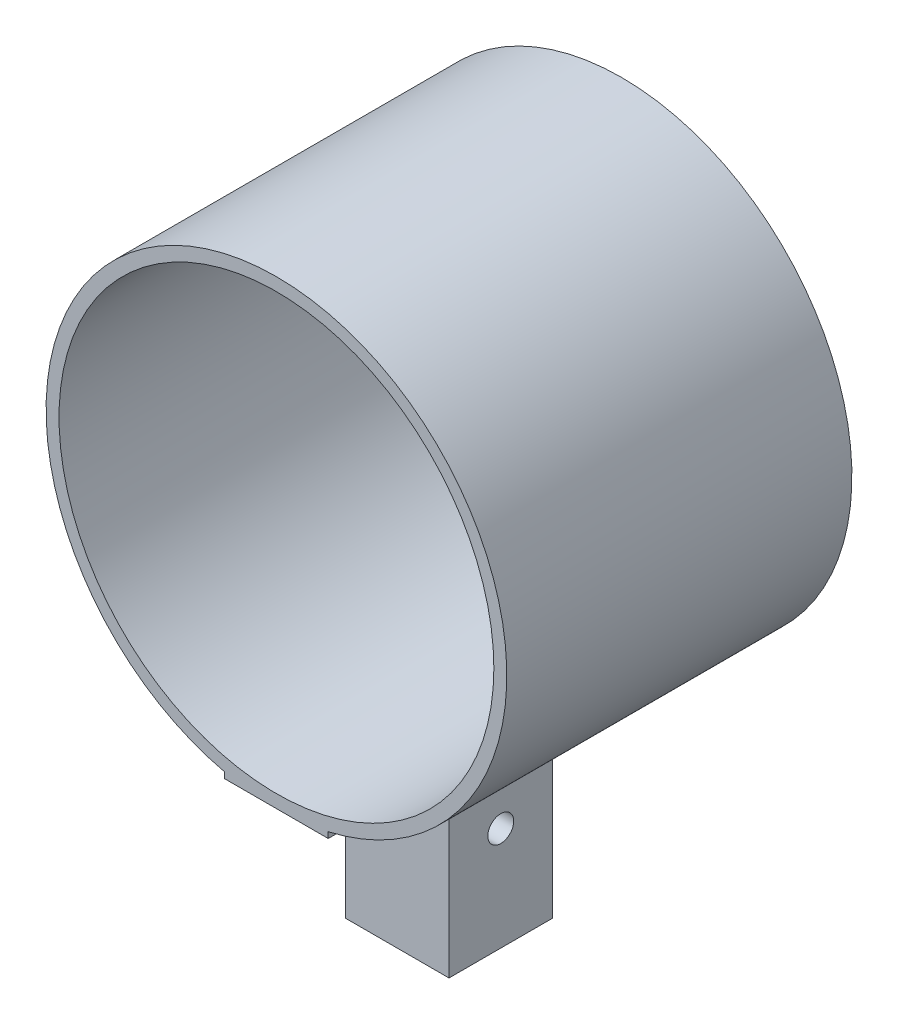
SolidWorks part; units mm, degrees
material "Polyetheretherketone (PEEK)"
ref_plane "Front Plane" through (0, 0, 0) normal (0, 0, 1) x (1, 0, 0)
ref_plane "Top Plane" through (0, 0, 0) normal (0, 1, 0) x (1, 0, 0)
ref_plane "Right Plane" through (0, 0, 0) normal (1, 0, 0) x (0, 0, -1)
sketch "Sketch1" plane through (0, 0, 0) normal (0, 0, 1) x (1, 0, 0)
  line L1 (-12.7, -56.515) -> (12.7, -56.515)
  line L2 (-12.7, -56.515) -> (-12.7, -55.0695)
  line L4 (12.7, -56.515) -> (12.7, -55.0695)
  line L5 (-12.7, -56.515) -> (12.7, -55.0695) construction
  line L6 (-12.7, -55.0695) -> (12.7, -56.515) construction
  arc A0 (12.7, -55.0695) -> (-12.7, -55.0695) centre (0, 0) ccw
  circle A1 centre (0, 0) radius 56.515 construction
  point P3 (0, -55.7923)
  dimension "SupportOutsideDiam" = 113.03
  dimension "PegWidth" = 25.4
  dimension "PegBaseHeight" = 1.4455
extrude "Boss-Extrude1" add sketch "Sketch1" along normal blind 84.6667
sketch "Sketch2" plane through (0, 0, 84.6667) normal (0, 0, 1) x (1, 0, 0)
  circle A0 centre (0, 0) radius 53.34
  dimension "SupportInsideDiam" = 106.68
extrude "Cut-Extrude1" cut sketch "Sketch2" against normal through all
sketch "Sketch3" plane through (0, -56.515, 0) normal (0, -1, 0) x (1, 0, 0)
  line L0 (12.7, 84.6667) -> (12.7, 0) construction
  line L1 (-12.7, 29.6333) -> (12.7, 29.6333)
  line L2 (-12.7, 29.6333) -> (-12.7, 55.0333)
  line L3 (-12.7, 55.0333) -> (12.7, 55.0333)
  line L4 (12.7, 29.6333) -> (12.7, 55.0333)
  line L5 (-12.7, 29.6333) -> (12.7, 55.0333) construction
  line L6 (-12.7, 55.0333) -> (12.7, 29.6333) construction
  line L7 (-12.7, 84.6667) -> (-12.7, 0) construction
  line L8 (-12.7, 0) -> (12.7, 0) construction
  point P0 (0, 42.3333)
  point P10 (-12.7, 42.3333)
  point P14 (0, 0)
extrude "Boss-Extrude2" add sketch "Sketch3" along normal blind 44.45
sketch "Sketch5" plane through (12.7, 0, 0) normal (1, 0, 0) x (0, 0, -1)
  line L0 (-29.6333, -100.965) -> (-55.0333, -100.965) construction
  line L1 (-84.6667, -56.515) -> (-55.0333, -56.515) construction
  circle A0 centre (-42.3333, -75.565) radius 3.175
  point P4 (-42.3333, -100.965)
  point P7 (-69.85, -56.515)
  dimension "D1" = 6.35
  dimension "D2" = 19.05
extrude "Cut-Extrude2" cut sketch "Sketch5" against normal through all
equation "\"ScopeLengthUnit\"= 10 * \"ScaleFactor\""
equation "\"EyepieceRadius\"= 0.75 * \"ScaleFactor\""
equation "\"ScopeThickness\"= 0.1 * \"ScaleFactor\""
equation "\"ScopeLensWidth\"= 2 * \"ScaleFactor\""
equation "\"ScopeOutsideRadius\"= 2.1 * \"ScaleFactor\""
equation "\"PegWidth\"=1"
equation "\"PegWidth@Sketch1\"=\"PegWidth\""
equation "\"SupportOutsideDiam\"= \"ScopeOutsideRadius\" * 2 + .25"
equation "\"SupportOutsideDiam@Sketch1\"=\"SupportOutsideDiam\""
equation "\"PegBaseHeight@Sketch1\" = ( \"SupportOutsideDiam\" / 2 ) - ( ( \"SupportOutsideDiam\" / 2 ) ^ 2 - ( \"PegWidth\" / 2 ) ^ 2 ) ^ ( 1 / 2 )"
equation "\"SupportInsideDiam@Sketch2\"=\"ScopeOutsideRadius\"*2"
equation "\"SupportThicknes@Boss-Extrude1\"=\"ScopeLengthUnit\"/3"
equation "\"RotatingDiskDiam\"=3"
equation "\"LegSeatWidth\"=4 "
equation "\"BoltCircleDiam\"= ( \"RotatingDiskDiam\" + \"RotatingDiskHousingDiameter\" ) / 2"
equation "\"RotatingDiskHousingDiameter\"= (\"RotatingDiskDiam\" + 2)"
equation "\"LegSeatHeight\"=2"
equation "\"LegThickness\"=0.25"
equation "\"LegHeight\"=48"
equation "\"LegBoltDiam\"=0.25"
equation "\"PinHeight\"=\"RotDiskLidHeight\" + \"RotDiskHeight\" + \"PinBoltDiam\"*3"
equation "\"D1@Boss-Extrude2\"=\"PinHeight\""
equation "\"PinBoltDiam\"=0.25"
equation "\"D1@Sketch5\"=\"PinBoltDiam\""
equation "\"RotDiskHeight\"=0.5"
equation "\"RotDiskLidHeight\"= 0.5"
equation "\"DiskSeatPinDiam\"=0.25"
equation "\"ScaleFactor\"= 1"
